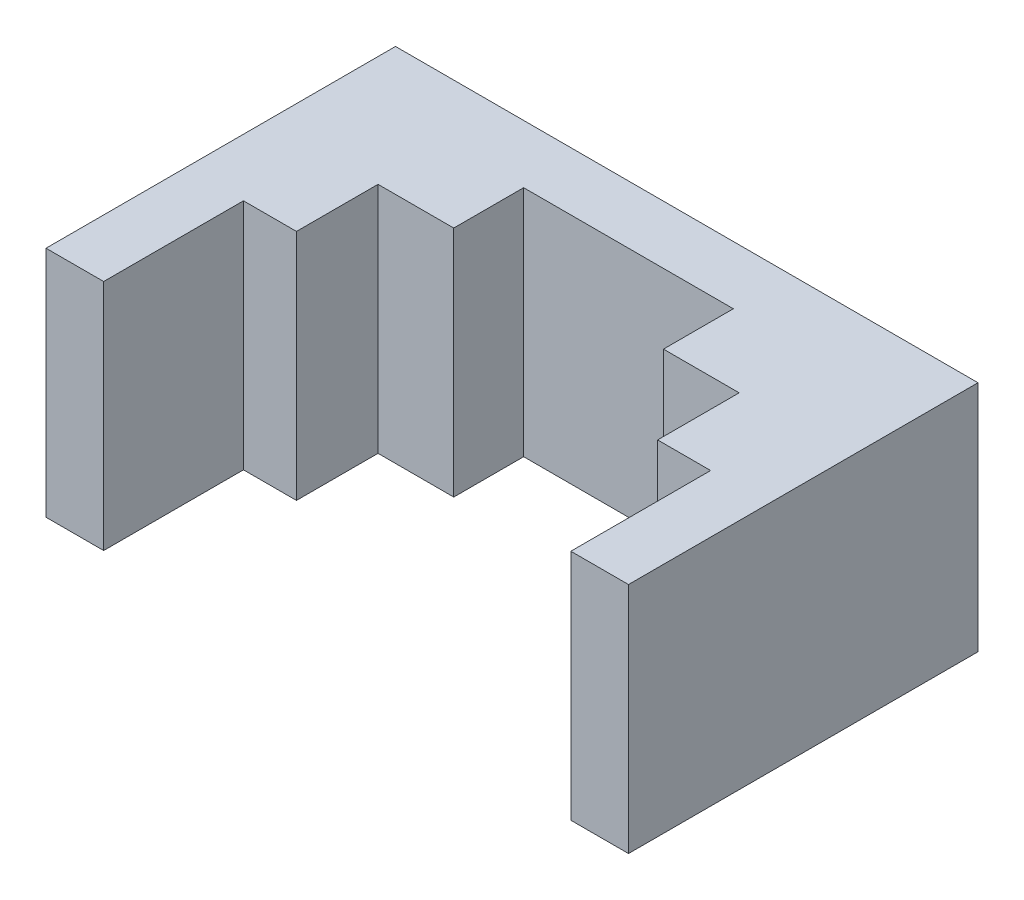
SolidWorks part; units mm, degrees
ref_plane "Front" through (0, 0, 0) normal (0, 0, 1) x (1, 0, 0)
ref_plane "Top" through (0, 0, 0) normal (0, 1, 0) x (1, 0, 0)
ref_plane "Right" through (0, 0, 0) normal (1, 0, 0) x (0, 0, -1)
other "Configuration Table"
sketch "Sketch1" plane through (0, 0, 0) normal (0, 0, 1) x (1, 0, 0)
  line L1 (-12.5, 5) -> (12.5, 5)
  line L2 (-12.5, 5) -> (-12.5, -5)
  line L3 (-12.5, -5) -> (12.5, -5)
  line L4 (12.5, 5) -> (12.5, -5)
  line L5 (-12.5, 5) -> (12.5, -5) construction
  line L6 (-12.5, -5) -> (12.5, 5) construction
  point P0 (0, 0)
extrude "Boss-Extrude1" add sketch "Sketch1" along normal blind 15
sketch "Sketch2" plane through (0, 0, 15) normal (0, 0, 1) x (1, 0, 0)
  line L0 (-12.5, -5) -> (12.5, -5) construction
  line L1 (-10.025, 5) -> (10.025, 5)
  line L2 (-10.025, 5) -> (-10.025, -5)
  line L3 (-10.025, -5) -> (10.025, -5)
  line L4 (10.025, 5) -> (10.025, -5)
  line L5 (-10.025, 5) -> (10.025, -5) construction
  line L6 (-10.025, -5) -> (10.025, 5) construction
  point P0 (0, 0)
extrude "Cut-Extrude1" cut sketch "Sketch2" against normal blind 6
sketch "Sketch3" plane through (0, 0, 9) normal (0, 0, 1) x (1, 0, 0)
  line L0 (-10.025, -5) -> (10.025, -5) construction
  line L1 (-4.5, 5) -> (4.5, 5)
  line L2 (-4.5, 5) -> (-4.5, -5)
  line L3 (-4.5, -5) -> (4.5, -5)
  line L4 (4.5, 5) -> (4.5, -5)
  line L5 (-4.5, 5) -> (4.5, -5) construction
  line L6 (-4.5, -5) -> (4.5, 5) construction
  point P0 (0, 0)
extrude "Cut-Extrude2" cut sketch "Sketch3" against normal blind 6.5
sketch "Sketch4" plane through (0, 0, 9) normal (0, 0, 1) x (1, 0, 0)
  line L0 (4.5, -5) -> (10.025, -5) construction
  line L1 (-7.75, 5) -> (7.75, 5)
  line L2 (-7.75, 5) -> (-7.75, -5)
  line L3 (-7.75, -5) -> (7.75, -5)
  line L4 (7.75, 5) -> (7.75, -5)
  line L5 (-7.75, 5) -> (7.75, -5) construction
  line L6 (-7.75, -5) -> (7.75, 5) construction
  point P0 (0, 0)
extrude "Cut-Extrude3" cut sketch "Sketch4" against normal blind 3.5
